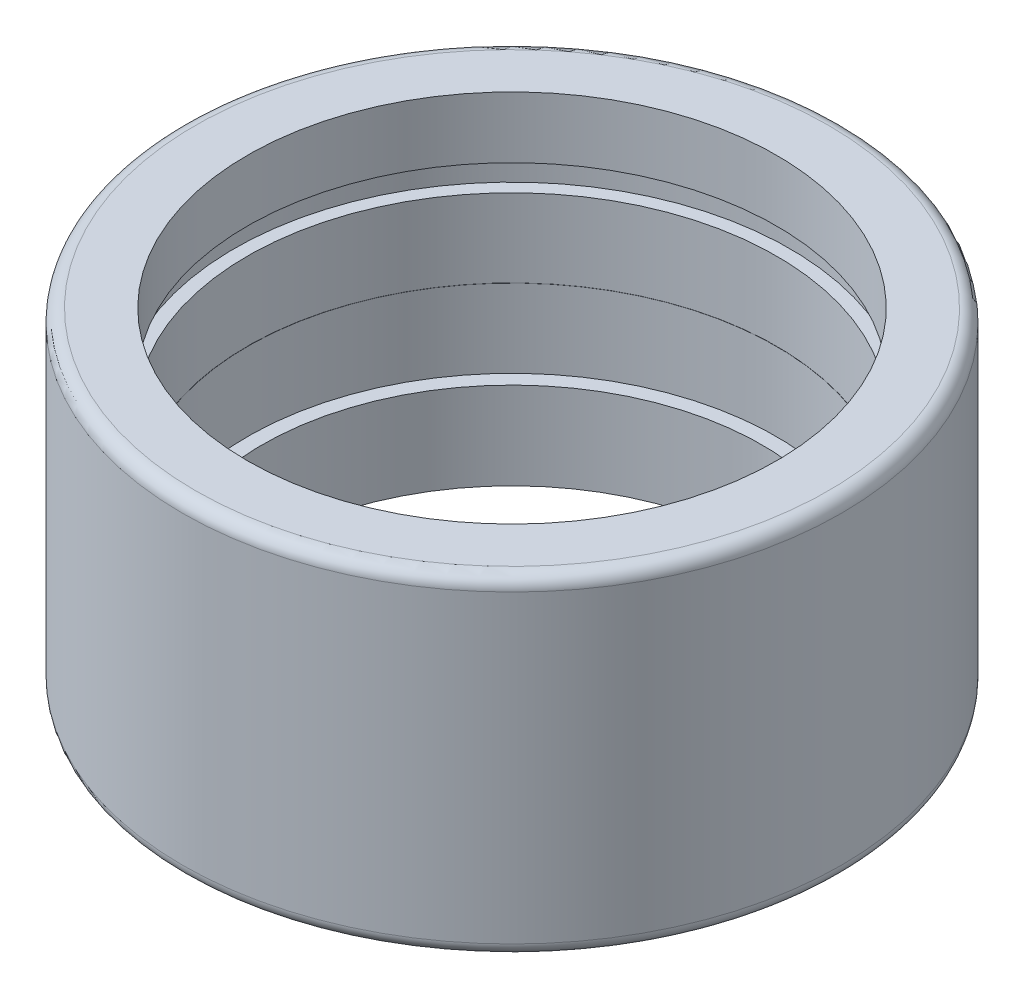
SolidWorks part; units mm, degrees
ref_plane "Front Plane" through (0, 0, 0) normal (0, 0, 1) x (1, 0, 0)
ref_plane "Top Plane" through (0, 0, 0) normal (0, 1, 0) x (1, 0, 0)
ref_plane "Right Plane" through (0, 0, 0) normal (1, 0, 0) x (0, 0, -1)
sketch "Sketch1" plane through (0, 0, 0) normal (0, 1, 0) x (1, 0, 0)
  circle A0 centre (0, 0) radius 12.65
  dimension "D1" = 25.3
extrude "Boss-Extrude1" add sketch "Sketch1" along normal mid plane 12.7
sketch "Sketch2" plane through (0, 0, 0) normal (0, 1, 0) x (1, 0, 0)
  circle A0 centre (0, 0) radius 9.6
  dimension "D1" = 19.2
extrude "Cut-Extrude1" cut sketch "Sketch2" against normal through all both and the other way through all
sketch "Sketch3" plane through (0, 0, 0) normal (0, 1, 0) x (1, 0, 0)
  circle A0 centre (0, 0) radius 10.1524
  dimension "D1" = 20.3048
extrude "Cut-Extrude2" cut sketch "Sketch3" against normal mid plane 6
sketch "Sketch4" plane through (0, 0, 0) normal (0, 1, 0) x (1, 0, 0)
  circle A0 centre (0, 0) radius 10.16
  dimension "D1" = 20.32
extrude "Cut-Extrude3" cut sketch "Sketch4" along normal blind 10.826
ref_plane "Plane2" through (0, 2.9972, 0) normal (0, 1, 0) x (1, 0, 0)
sketch "Sketch6" plane through (0, 2.9972, 0) normal (0, 1, 0) x (1, 0, 0)
  circle A0 centre (0, 0) radius 10.6604
  dimension "D1" = 21.3208
extrude "Cut-Extrude4" cut sketch "Sketch6" along normal blind 1
fillet "Fillet1" radius 0.5 2 edges at (0, -6.35, 12.65) (0, 6.35, 12.65)
